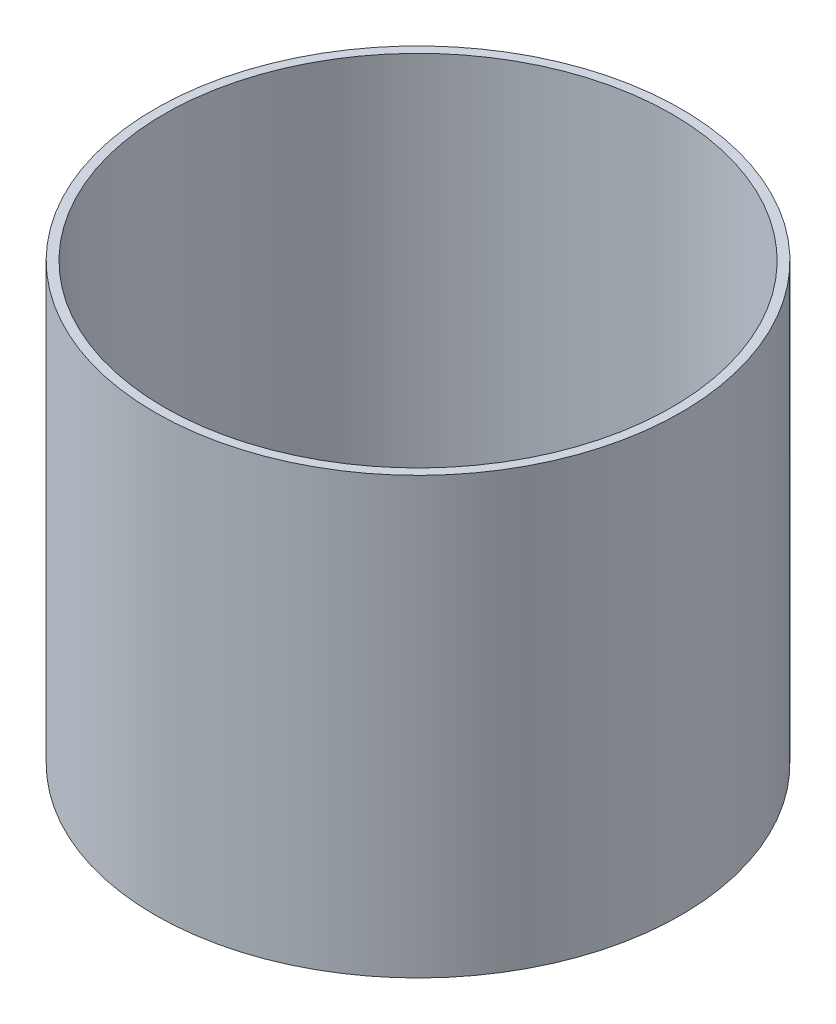
SolidWorks part; units mm, degrees
ref_plane "Front Plane" through (0, 0, 0) normal (0, 0, 1) x (1, 0, 0)
ref_plane "Top Plane" through (0, 0, 0) normal (0, 1, 0) x (1, 0, 0)
ref_plane "Right Plane" through (0, 0, 0) normal (1, 0, 0) x (0, 0, -1)
sketch "Sketch1" plane through (0, 0, 0) normal (0, 1, 0) x (1, 0, 0)
  circle A0 centre (0, 0) radius 88.9
  circle A1 centre (0, 0) radius 92.075
  dimension "D1" = 177.8
  dimension "D2" = 184.15
extrude "Boss-Extrude1" add sketch "Sketch1" along normal blind 152.4
